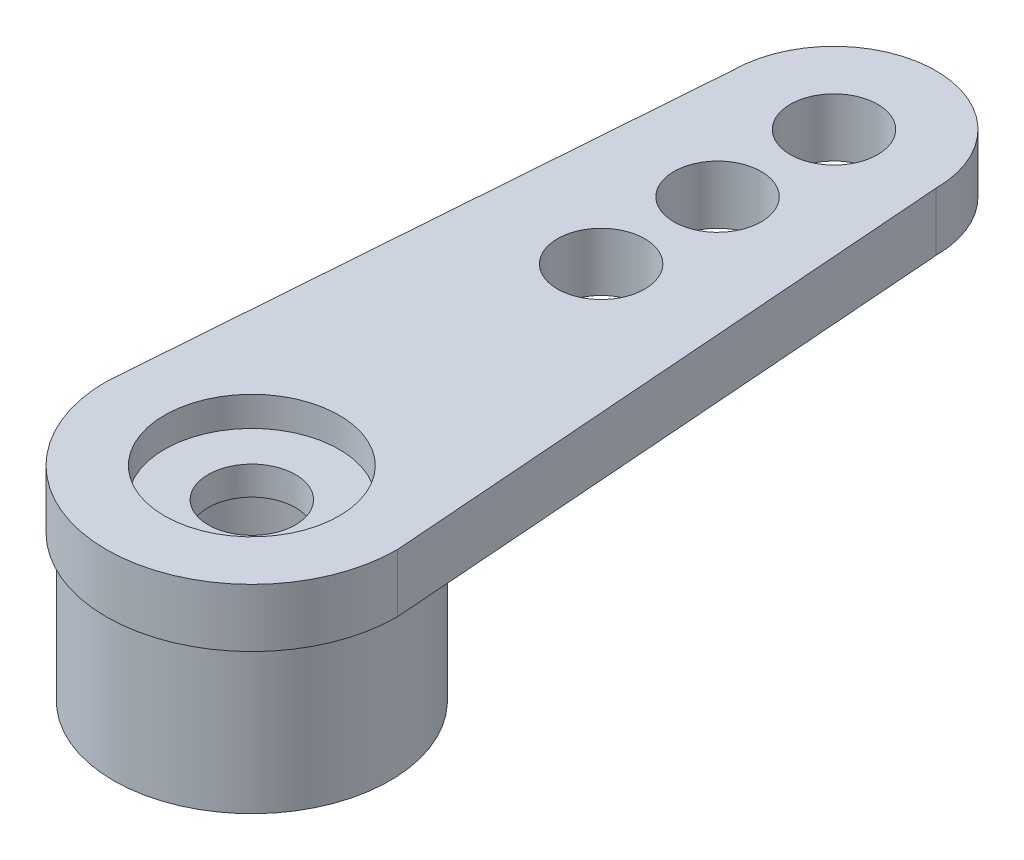
SolidWorks part; units mm, degrees
ref_plane "Front Plane" through (0, 0, 0) normal (0, 0, 1) x (1, 0, 0)
ref_plane "Top Plane" through (0, 0, 0) normal (0, 1, 0) x (1, 0, 0)
ref_plane "Right Plane" through (0, 0, 0) normal (1, 0, 0) x (0, 0, -1)
sketch "Sketch1" plane through (0, 0, 0) normal (0, 1, 0) x (1, 0, 0)
  line L0 (3.5, 20) -> (5, 0)
  line L5 (-3.5, 20) -> (-5, 0)
  arc A0 (-5, 0) -> (5, 0) centre (0, 0) ccw
  arc A2 (3.5, 20) -> (-3.5, 20) centre (0, 20) ccw
  dimension "D1" = 10
  dimension "D2" = 7
  dimension "D3" = 20
extrude "Boss-Extrude1" add sketch "Sketch1" along normal blind 2
sketch "Sketch2" plane through (0, 2, 0) normal (0, 1, 0) x (1, 0, 0)
  line L0 (0, 0) -> (0, 20) construction
  circle A0 centre (0, 20) radius 1.5
  dimension "D1" = 3
  dimension "D2" = 20
extrude "Cut-Extrude1" cut sketch "Sketch2" against normal through all
sketch "Sketch7" plane through (0, 0, 0) normal (0, -1, 0) x (-1, 0, 0)
  circle A0 centre (0, 0) radius 4.75
  dimension "D1" = 9.5
extrude "Boss-Extrude2" add sketch "Sketch7" along normal blind 5
sketch "Sketch3" plane through (0, 2, 0) normal (0, 1, 0) x (1, 0, 0)
  circle A0 centre (0, 0) radius 1.5
  dimension "D1" = 3
extrude "Cut-Extrude2" cut sketch "Sketch3" against normal through all
sketch "Sketch4" plane through (0, 2, 0) normal (0, 1, 0) x (1, 0, 0)
  circle A0 centre (0, 0) radius 3
  dimension "D1" = 6
extrude "Cut-Extrude3" cut sketch "Sketch4" against normal blind 1.016
sketch "Sketch6" plane through (0, 2, 0) normal (0, 1, 0) x (1, 0, 0)
  circle A0 centre (0, 16) radius 1.5
  dimension "D1" = 3
  dimension "D2" = 16
extrude "Cut-Extrude4" cut sketch "Sketch6" against normal through all
sketch "Sketch5" plane through (0, 2, 0) normal (0, 1, 0) x (1, 0, 0)
  circle A0 centre (0, 12) radius 1.5
  dimension "D2" = 3
  dimension "D1" = 12
extrude "Cut-Extrude5" cut sketch "Sketch5" against normal through all
sketch "Sketch8" plane through (0, -5, 0) normal (0, -1, 0) x (-1, 0, 0)
  circle A0 centre (0, 0) radius 3
  dimension "D1" = 6
extrude "Cut-Extrude6" cut sketch "Sketch8" against normal blind 5
